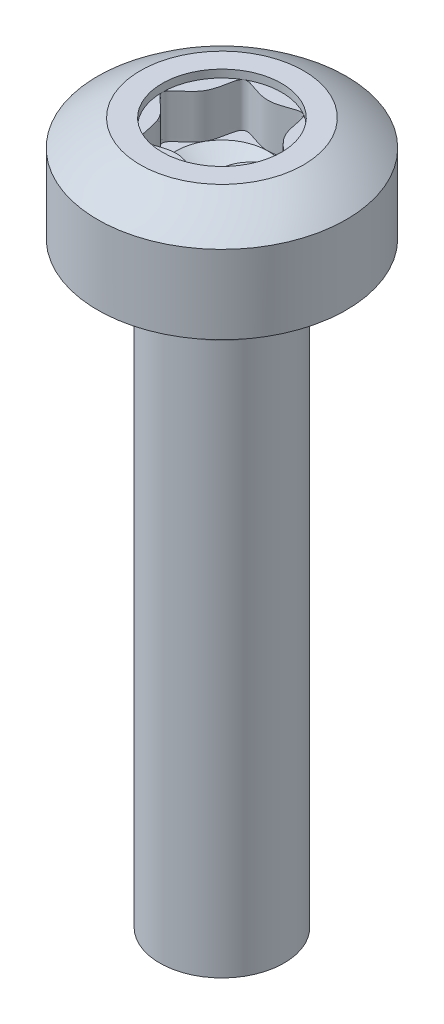
SolidWorks part; units mm, degrees
material "AISI 316L Acero inoxidable"
ref_plane "Front" through (0, 0, 0) normal (0, 0, 1) x (1, 0, 0)
ref_plane "Top" through (0, 0, 0) normal (0, 1, 0) x (1, 0, 0)
ref_plane "Right" through (0, 0, 0) normal (1, 0, 0) x (0, 0, -1)
sketch "Sketch1" plane through (0, 0, 0) normal (0, 0, 1) x (1, 0, 0)
  line L0 (0, 0) -> (0, 34.6184) construction
  line L1 (0, 0) -> (1.25, 0)
  line L2 (1.25, 0) -> (1.25, 12)
  line L3 (1.25, 12) -> (2.5, 12)
  line L4 (2.5, 12) -> (2.5, 14.1)
  line L5 (2.5, 14.1) -> (0, 14.1)
  line L6 (0, 14.1) -> (0, 0)
  line L7 (2.5, 12) -> (2.95, 12) construction
  line L8 (2.95, 12) -> (2.95, 0.9) construction
  dimension "HEAD_DIA" = 5
  dimension "HEAD_HT" = 2.1
  dimension "LENGTH" = 12
  dimension "DIA" = 2.5
  dimension "pitch" = 0.45
  dimension "thread_length" = 11.1
revolve "BODY" add sketch "Sketch1" angle 360 about L0
cosmetic thread "ThreadCosmetic" [suppressed] parameters "D1"=11.1, "D2"=2.0129
sketch "Sketch2" plane through (0, 0, 0) normal (0, 0, 1) x (1, 0, 0)
  line L0 (2.5, 13.575) -> (0, 10.4525) construction
  line L3 (2.5, 12) -> (2.5, 14.1) construction
  line L4 (0, 0) -> (0, 34.6184) construction
  line L5 (0, 14.4525) -> (0, 14.9347)
  line L6 (4, 10.4525) -> (4, 14.9347)
  line L7 (4, 14.9347) -> (0, 14.9347)
  line L8 (0, 14.9347) -> (4, 14.9347)
  arc A0 (4, 10.4525) -> (0, 14.4525) centre (0, 10.4525) ccw
  dimension "SPHERE_DIA" = 4
  dimension "D1" = 0.525
  dimension "D2" = 0.4822
revolve "HEAD-CUT" cut sketch "Sketch2" angle 360 about axis through (0, 0, 0) along (0, 1, 0)
sketch "Sketch4" plane through (0, 0, 0) normal (0, 0, 1) x (1, 0, 0)
  line L0 (-1.25, 11.1) -> (-1.1886, 11.9)
  line L1 (-1.25, 12) -> (-1.25, 0) construction
  line L2 (-1.25, 12) -> (-1.25, 11.1)
  arc A0 (-1.1886, 11.9) -> (-1.25, 12) centre (-1.2884, 11.9076) ccw
  dimension "CONER_RAD" = 0.1
  dimension "D1" = 0.1
  dimension "GAP" = 0.9
revolve "GAP" cut sketch "Sketch4" angle 360 about axis through (0, 0, 0) along (0, 1, 0)
sketch "Sketch5" plane through (0, 14.1, 0) normal (0, 1, 0) x (-1, 0, 0)
  line L0 (0, 0.9231) -> (0, 0) construction
  line L1 (0, 0) -> (0.6, 1.0392) construction
  line L2 (0.6, 1.0392) -> (-0.6, 1.0392) construction
  line L3 (-0.6, 1.0392) -> (-1.2, 0) construction
  line L4 (-1.2, 0) -> (-0.6, -1.0392) construction
  line L5 (-0.6, -1.0392) -> (0.6, -1.0392) construction
  line L6 (0.6, -1.0392) -> (1.2, 0) construction
  line L7 (1.2, 0) -> (0.6, 1.0392) construction
  line L8 (0, 0.9231) -> (-0.7994, 0.4615) construction
  line L9 (-0.7994, 0.4615) -> (-0.7994, -0.4615) construction
  line L10 (-0.7994, -0.4615) -> (0, -0.9231) construction
  line L11 (0, -0.9231) -> (0.7994, -0.4615) construction
  line L12 (0.7994, -0.4615) -> (0.7994, 0.4615) construction
  line L13 (0.7994, 0.4615) -> (0, 0.9231) construction
  circle A0 centre (0, 0) radius 0.9231 construction
  circle A1 centre (0, 0) radius 1.2
  spline S0 degree 3 poles (0.7387, 1.2795) (0, 0.7449) (-0.7387, 1.2795) (-0.6451, 0.3724) (-1.4775, 0) (-0.6451, -0.3724) (-0.7387, -1.2795) (0, -0.7449) (0.7387, -1.2795) (0.6451, -0.3724) (1.4775, 0) (0.6451, 0.3724) (0.7387, 1.2795) (0, 0.7449) (-0.7387, 1.2795) knots -0.25 -0.166667 -0.083333 0 0.083333 0.166667 0.25 0.333333 0.416667 0.5 0.583333 0.666667 0.75 0.833333 0.916667 1 1.083333 1.166667 1.25 only from (0, 0.9231) to (0, 0.9231)
  dimension "slot_dia" = 2.4
  dimension "D3" = 1.8462
  dimension "D1" = 30
extrude "Recess-Cut-Extrude1" cut sketch "Sketch5" against normal blind 1.04
sketch "Sketch3" plane through (0, 0, 0) normal (0, 0, 1) x (1, 0, 0)
  line L0 (0, 12.5271) -> (0.9231, 13.06)
  line L1 (0, 0) -> (0, 34.6184) construction
  line L2 (0.9231, 13.06) -> (0, 13.06)
  line L3 (0, 13.06) -> (0, 12.5271)
  dimension "D1" = 60
  dimension "DRILL_RAD" = 0.9231
  dimension "SLOT_DEP" = 1.04
revolve "DRILL-CUT" cut sketch "Sketch3" angle 360 about axis through (0, 0, 0) along (0, 1, 0)
sketch "Sketch6" plane through (0, 0, 0) normal (0, 0, 1) x (1, 0, 0)
  line L0 (1.25, 0) -> (1.0064, 0.1406)
  line L1 (1.0064, 0.1406) -> (1.25, 0.2812)
  line L4 (1.25, 0.2812) -> (1.25, 0)
  line L5 (0, 0) -> (0, 34.6184) construction
  dimension "D1" = 1.0064
revolve "ThreadSchematic" [suppressed] cut sketch "Sketch6" angle 360 about axis through (0, 0, 0) along (0, 1, 0)
pattern_linear "ThdSchPat" [suppressed] count 25 spacing 0.45 along (0, 1, 0)
sketch "Sketch7" plane through (0, 14.1, 0) normal (0, 1, 0) x (-1, 0, 0)
  circle A0 centre (0, 0) radius 1.2
  dimension "D1" = 2.4
extrude "Recess-Cut-Extrude2" cut sketch "Sketch7" against normal blind 0.156
equation "\"D1@Sketch2\" = \"HEAD_HT@Sketch1\" * 0.25"
equation "\"D1@Sketch4\" = \"CONER_RAD@Sketch4\""
equation "\"D1@Recess-Cut-Extrude1\" = \"SLOT_DEP@Sketch3\""
equation "\"D1@Sketch7\" = \"slot_dia@Sketch5\""
equation "\"D1@Recess-Cut-Extrude2\" = \"SLOT_DEP@Sketch3\" * 0.15"
equation "\"D3@Sketch5\" = \"slot_dia@Sketch5\" / 1.3"
equation "\"DRILL_RAD@Sketch3\" = \"D3@Sketch5\" * 0.5"
equation "\"D1@ThreadCosmetic\" = \"thread_length@Sketch1\""
equation "\"D2@ThreadCosmetic\" = \"DIA@Sketch1\" - 1.0825 * \"pitch@Sketch1\""
equation "\"D1@Sketch6\" = \"D2@ThreadCosmetic\" / 2"
equation "\"D3@ThdSchPat\" = \"pitch@Sketch1\""
equation "\"D1@ThdSchPat\" = \"thread_length@Sketch1\" / \"pitch@Sketch1\""
